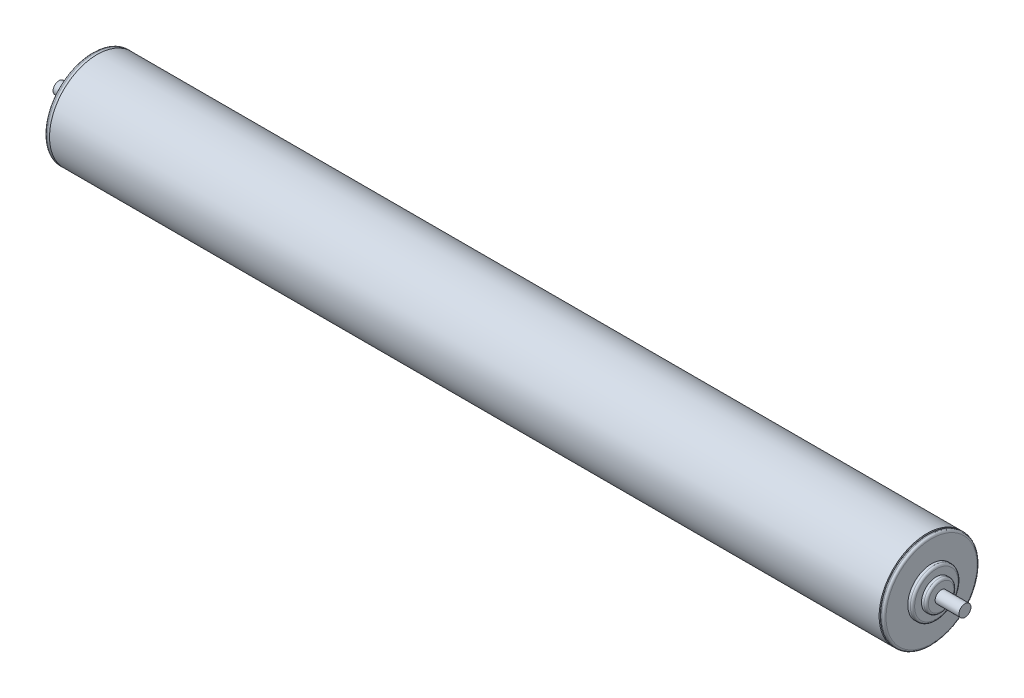
SolidWorks part; units mm, degrees
ref_plane "Front Plane" through (0, 0, 0) normal (0, 0, 1) x (1, 0, 0)
ref_plane "Top Plane" through (0, 0, 0) normal (0, 1, 0) x (1, 0, 0)
ref_plane "Right Plane" through (0, 0, 0) normal (1, 0, 0) x (0, 0, -1)
sketch "Sketch1" plane through (0, 0, 0) normal (0, 0, 1) x (1, 0, 0)
  line L0 (-228.6, 0) -> (228.6, 0) construction
  line L1 (228.6, 0) -> (241.3, 0) construction
  line L2 (-228.6, 0) -> (-241.3, 0) construction
  line L3 (-241.3, 3.175) -> (-241.3, -3.175) construction
  line L4 (0, 25.4) -> (0, -25.4) construction
  line L5 (-228.6, 0) -> (-228.6, 7.9375)
  line L6 (-228.6, 7.9375) -> (-226.06, 7.9375)
  line L7 (-226.06, 7.9375) -> (-226.06, 12.7)
  line L8 (-226.06, 12.7) -> (-223.52, 12.7)
  line L9 (-223.52, 12.7) -> (-223.52, 25.4)
  line L10 (-223.52, 25.4) -> (-220.98, 25.4)
  line L11 (-220.98, 25.4) -> (-220.98, 0)
  line L12 (-228.6, 0) -> (-220.98, 0)
  dimension "D1" = 6.35
  dimension "D2" = 50.8
  dimension "BF" = 457.2
  dimension "D4" = 482.6
  dimension "D5" = 15.875
  dimension "D6" = 25.4
  dimension "D7" = 50.8
  dimension "D8" = 7.62
revolve "Revolve1" add sketch "Sketch1" angle 360 mid plane about L0
fillet "Fillet1" radius 1.143 4 edges at (-226.06, 0, 12.7) (-228.6, 0, 7.9375) (-220.98, 0, 25.4) (-223.52, 0, 25.4)
sketch "Sketch2" plane through (-228.6, 0, 0) normal (-1, 0, 0) x (0, 0, 1)
  circle A0 centre (0, 0) radius 3.175
extrude "Boss-Extrude1" add sketch "Sketch2" along normal up to vertex
mirror "Mirror2" about plane through (0, 0, 0) normal (1, 0, 0) of bodies 102
sketch "Sketch3" plane through (0, 0, 0) normal (1, 0, 0) x (0, 0, -1)
  circle A0 centre (0, 0) radius 25.4
extrude "Boss-Extrude2" add sketch "Sketch3" against normal up to surface and the other way up to surface
equation "\"D4@Sketch1\" = \"BF@Sketch1\"+1"
